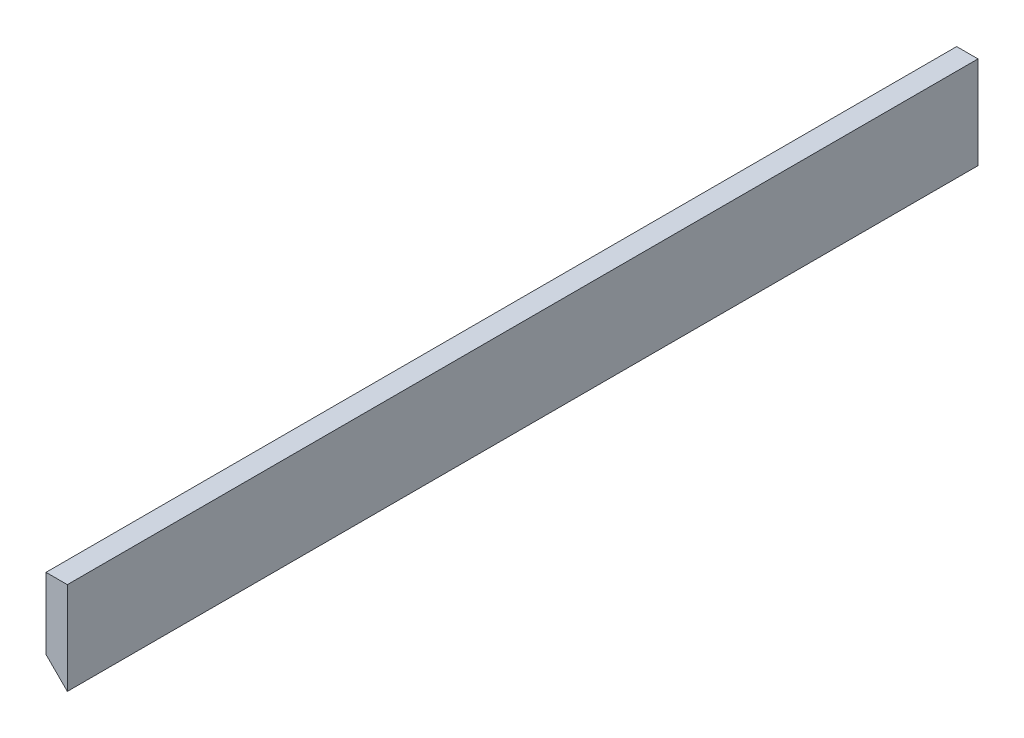
SolidWorks part; units mm, degrees
ref_plane "Plan de face" through (0, 0, 0) normal (0, 0, 1) x (1, 0, 0)
ref_plane "Plan de dessus" through (0, 0, 0) normal (0, 1, 0) x (1, 0, 0)
ref_plane "Plan de droite" through (0, 0, 0) normal (1, 0, 0) x (0, 0, -1)
sketch "Esquisse1" plane through (0, 0, 0) normal (0, 0, 1) x (1, 0, 0)
  line L0 (0, 0) -> (0, 65)
  line L1 (0, 65) -> (-15, 65)
  line L2 (-15, 65) -> (-15, 15)
  line L3 (-15, 15) -> (0, 0)
  dimension "D1" = 15
  dimension "D2" = 45
  dimension "D3" = 50
extrude "Boss.-Extru.1" add sketch "Esquisse1" along normal blind 640
